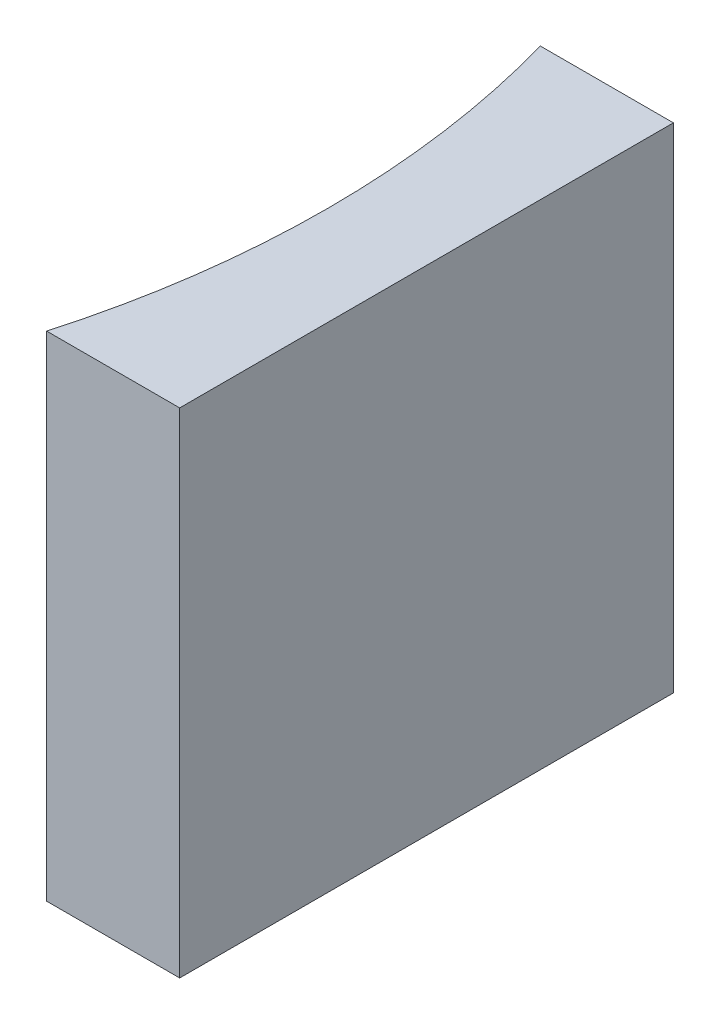
SolidWorks part; units mm, degrees
ref_plane "前视基准面" through (0, 0, 0) normal (0, 0, 1) x (1, 0, 0)
ref_plane "上视基准面" through (0, 0, 0) normal (0, 1, 0) x (1, 0, 0)
ref_plane "右视基准面" through (0, 0, 0) normal (1, 0, 0) x (0, 0, -1)
sketch "草图1" plane through (0, 0, 0) normal (0, 1, 0) x (1, 0, 0)
  line L0 (0, 0) -> (0, -10)
  line L1 (0, 0) -> (-2.6955, 0)
  line L2 (0, -10) -> (-2.6955, -10)
  line L3 (2.135, -5) -> (-21.2259, -5) construction
  arc A0 (-2.6955, -10) -> (-2.6955, 0) centre (-20.32, -5) ccw
  point P7 (-2, -5)
  point P8 (0, -5)
  point P10 (2.135, -5)
  dimension "D2" = 18.32
  dimension "D3" = 2
  dimension "D1" = 10
extrude "凸台-拉伸1" add sketch "草图1" along normal blind 10
